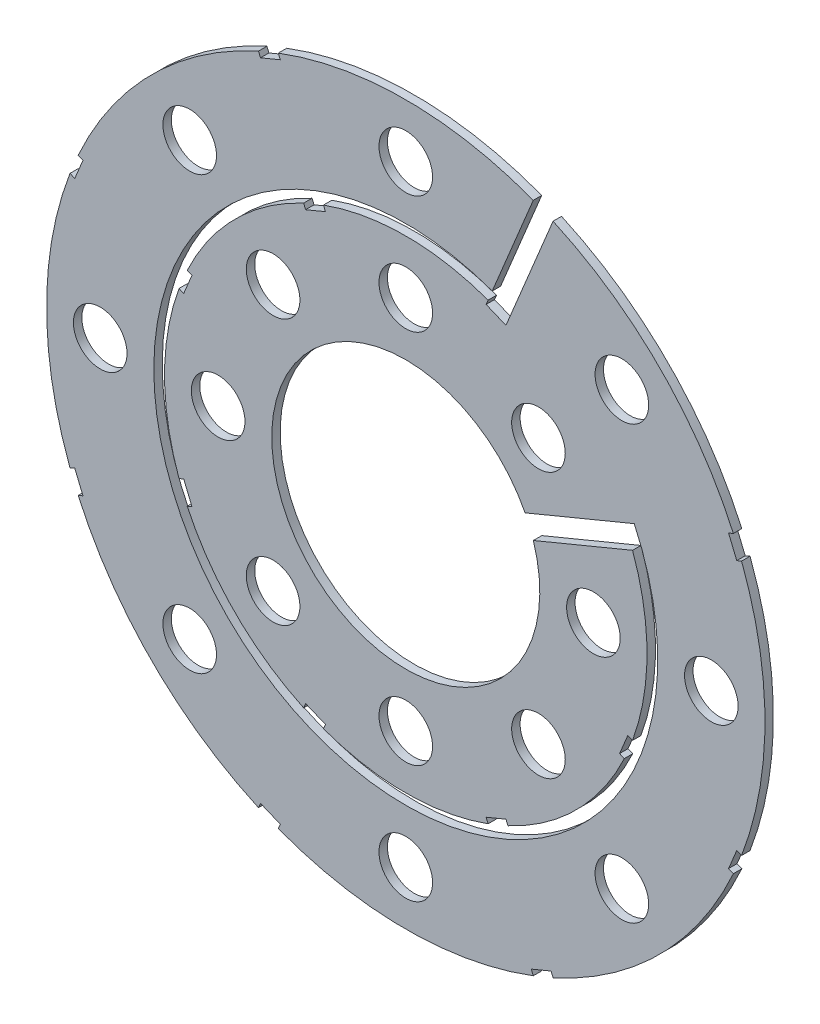
SolidWorks part; units mm, degrees
material "Copper"
ref_plane "Front Plane" through (0, 0, 0) normal (0, 0, 1) x (1, 0, 0)
ref_plane "Top Plane" through (0, 0, 0) normal (0, 1, 0) x (1, 0, 0)
ref_plane "Right Plane" through (0, 0, 0) normal (1, 0, 0) x (0, 0, -1)
sketch "Sketch1" plane through (0, 0, 0) normal (0, 0, 1) x (1, 0, 0)
  line L0 (0, 0) -> (101.6, 0) construction
  line L1 (0, 0) -> (93.8662, 38.8806) construction
  line L2 (0, 0) -> (38.8806, 93.8662) construction
  line L3 (10.2375, 28.0342) -> (15.1007, 39.7749)
  line L4 (12.0977, 25.8878) -> (17.4473, 38.8029)
  line L5 (14.1336, 7.229) -> (27.0622, 12.5842)
  line L6 (15.1056, 4.8823) -> (26.8598, 9.751)
  arc A0 (15.1056, 4.8823) -> (14.1336, 7.229) centre (0, 0) cw
  arc A1 (26.8598, 9.751) -> (12.0977, 25.8878) centre (0, 0) cw
  arc A2 (27.0622, 12.5842) -> (10.2375, 28.0342) centre (0, 0) cw
  arc A3 (17.4473, 38.8029) -> (15.1007, 39.7749) centre (0, 0) cw
  dimension "D4" = 1.27
  dimension "D12" = 1.27
  dimension "D1" = 22.5
  dimension "D2" = 67.5
  dimension "D3" = 1.27
  dimension "D5" = 15.875
  dimension "D11" = 1.27
  dimension "D8" = 12.7
  dimension "D14" = 12.7
  dimension "D6" = 1.27
  dimension "D7" = 1.27
  dimension "D9" = 1.27
  dimension "D10" = 1.27
  dimension "D13" = 1.27
extrude "Boss-Extrude1" add sketch "Sketch1" along normal blind 1
sketch "Sketch2" plane through (0, 0, 1) normal (0, 0, 1) x (1, 0, 0)
  line L0 (0, 0) -> (36.195, 0) construction
  line L1 (0, 0) -> (25.5937, 25.5937) construction
  line L2 (0, 0) -> (25.5937, -25.5937) construction
  circle A0 centre (22.225, 0) radius 3.175
  arc A1 (14.1336, 7.229) -> (15.1056, 4.8823) centre (0, 0) ccw construction
  circle A2 centre (36.195, 0) radius 3.175
  arc A3 (10.2375, 28.0342) -> (27.0622, 12.5842) centre (0, 0) ccw construction
  circle A4 centre (15.7154, -15.7154) radius 3.175
  circle A5 centre (25.5937, -25.5937) radius 3.175
  circle A6 centre (0, -22.225) radius 3.175
  circle A7 centre (0, -36.195) radius 3.175
  circle A8 centre (-15.7154, -15.7154) radius 3.175
  circle A9 centre (-25.5937, -25.5937) radius 3.175
  circle A10 centre (-22.225, 0) radius 3.175
  circle A11 centre (-36.195, 0) radius 3.175
  circle A12 centre (-15.7154, 15.7154) radius 3.175
  circle A13 centre (-25.5937, 25.5937) radius 3.175
  circle A14 centre (0, 22.225) radius 3.175
  circle A15 centre (0, 36.195) radius 3.175
  circle A16 centre (15.7154, 15.7154) radius 3.175
  circle A17 centre (25.5937, 25.5937) radius 3.175
  arc A18 (15.1007, 39.7749) -> (17.4473, 38.8029) centre (0, 0) ccw construction
  point P40 (0, 0)
  dimension "D1" = 6.35
  dimension "D2" = 6.35
  dimension "D3" = 6.35
  dimension "D4" = 6.35
  dimension "D8" = 6.35
  dimension "D9" = 6.35
  dimension "D6" = 45
  dimension "D7" = 45
  dimension "D5" = 8
extrude "Cut-Extrude1" cut sketch "Sketch2" against normal through all
sketch "Sketch3" plane through (0, 0, 1) normal (0, 0, 1) x (1, 0, 0)
  line L0 (0, 0) -> (36.195, 0) construction
  line L1 (0, 0) -> (39.3065, -16.2813) construction
  line L2 (25.3272, -11.8655) -> (26.5005, -12.3515)
  line L3 (25.3272, -11.8655) -> (26.2992, -9.5188)
  line L4 (26.5005, -12.3515) -> (27.4725, -10.0049)
  line L5 (26.2992, -9.5188) -> (27.4725, -10.0049)
  line L6 (25.3272, -11.8655) -> (27.4725, -10.0049) construction
  line L7 (26.5005, -12.3515) -> (26.2992, -9.5188) construction
  line L8 (10.0049, -27.4725) -> (12.3515, -26.5005)
  line L9 (11.8655, -25.3272) -> (12.3515, -26.5005)
  line L10 (9.5188, -26.2992) -> (11.8655, -25.3272)
  line L11 (9.5188, -26.2992) -> (10.0049, -27.4725)
  line L12 (-12.3515, -26.5005) -> (-10.0049, -27.4725)
  line L13 (-9.5188, -26.2992) -> (-10.0049, -27.4725)
  line L14 (-11.8655, -25.3272) -> (-9.5188, -26.2992)
  line L15 (-11.8655, -25.3272) -> (-12.3515, -26.5005)
  line L16 (-27.4725, -10.0049) -> (-26.5005, -12.3515)
  line L17 (-25.3272, -11.8655) -> (-26.5005, -12.3515)
  line L18 (-26.2992, -9.5188) -> (-25.3272, -11.8655)
  line L19 (-26.2992, -9.5188) -> (-27.4725, -10.0049)
  line L20 (-26.5005, 12.3515) -> (-27.4725, 10.0049)
  line L21 (-26.2992, 9.5188) -> (-27.4725, 10.0049)
  line L22 (-25.3272, 11.8655) -> (-26.2992, 9.5188)
  line L23 (-25.3272, 11.8655) -> (-26.5005, 12.3515)
  line L24 (-10.0049, 27.4725) -> (-12.3515, 26.5005)
  line L25 (-11.8655, 25.3272) -> (-12.3515, 26.5005)
  line L26 (-9.5188, 26.2992) -> (-11.8655, 25.3272)
  line L27 (-9.5188, 26.2992) -> (-10.0049, 27.4725)
  line L28 (12.3515, 26.5005) -> (10.0049, 27.4725)
  line L29 (9.5188, 26.2992) -> (10.0049, 27.4725)
  line L30 (11.8655, 25.3272) -> (9.5188, 26.2992)
  line L31 (11.8655, 25.3272) -> (12.3515, 26.5005)
  line L32 (0, 0) -> (26.2992, -9.5188) construction
  line L33 (0, 0) -> (11.8655, -25.3272) construction
  line L34 (17.4473, 38.8029) -> (12.0977, 25.8878) construction
  line L35 (0, 0) -> (39.3065, 16.2813) construction
  line L36 (39.2058, 14.8649) -> (40.3791, 15.3509)
  line L37 (39.2058, 14.8649) -> (38.2338, 17.2116)
  line L38 (40.3791, 15.3509) -> (39.4071, 17.6976)
  line L39 (38.2338, 17.2116) -> (39.4071, 17.6976)
  line L40 (39.2058, 14.8649) -> (39.4071, 17.6976) construction
  line L41 (40.3791, 15.3509) -> (38.2338, 17.2116) construction
  line L42 (39.2058, -14.8649) -> (40.3791, -15.3509)
  line L43 (39.4071, -17.6976) -> (40.3791, -15.3509)
  line L44 (38.2338, -17.2116) -> (39.2058, -14.8649)
  line L45 (38.2338, -17.2116) -> (39.4071, -17.6976)
  line L46 (17.2116, -38.2338) -> (17.6976, -39.4071)
  line L47 (15.3509, -40.3791) -> (17.6976, -39.4071)
  line L48 (14.8649, -39.2058) -> (17.2116, -38.2338)
  line L49 (14.8649, -39.2058) -> (15.3509, -40.3791)
  line L50 (-14.8649, -39.2058) -> (-15.3509, -40.3791)
  line L51 (-17.6976, -39.4071) -> (-15.3509, -40.3791)
  line L52 (-17.2116, -38.2338) -> (-14.8649, -39.2058)
  line L53 (-17.2116, -38.2338) -> (-17.6976, -39.4071)
  line L54 (-38.2338, -17.2116) -> (-39.4071, -17.6976)
  line L55 (-40.3791, -15.3509) -> (-39.4071, -17.6976)
  line L56 (-39.2058, -14.8649) -> (-38.2338, -17.2116)
  line L57 (-39.2058, -14.8649) -> (-40.3791, -15.3509)
  line L58 (-39.2058, 14.8649) -> (-40.3791, 15.3509)
  line L59 (-39.4071, 17.6976) -> (-40.3791, 15.3509)
  line L60 (-38.2338, 17.2116) -> (-39.2058, 14.8649)
  line L61 (-38.2338, 17.2116) -> (-39.4071, 17.6976)
  line L62 (-17.2116, 38.2338) -> (-17.6976, 39.4071)
  line L63 (-15.3509, 40.3791) -> (-17.6976, 39.4071)
  line L64 (-14.8649, 39.2058) -> (-17.2116, 38.2338)
  line L65 (-14.8649, 39.2058) -> (-15.3509, 40.3791)
  line L66 (0, 0) -> (39.2058, 14.8649) construction
  line L67 (0, 0) -> (38.2338, -17.2116) construction
  arc A0 (15.1007, 39.7749) -> (17.4473, 38.8029) centre (0, 0) ccw construction
  arc A1 (12.0977, 25.8878) -> (26.8598, 9.751) centre (0, 0) ccw construction
  point P9 (26.3999, -10.9352)
  point P47 (39.3065, 16.2813)
  dimension "D1" = 22.5
  dimension "D2" = 1.27
  dimension "D3" = 2.54
  dimension "D4" = 1.27
  dimension "D5" = 0.635
  dimension "D7" = 45
  dimension "D8" = 0.635
  dimension "D9" = 67.5
  dimension "D10" = 2.54
  dimension "D11" = 22.5
  dimension "D12" = 1.27
  dimension "D13" = 2.54
  dimension "D14" = 0.635
  dimension "D15" = 1.27
  dimension "D17" = 45
  dimension "D18" = 112.5
  dimension "D19" = 0.635
  dimension "D6" = 7
  dimension "D16" = 7
extrude "Cut-Extrude2" cut sketch "Sketch3" against normal through all
